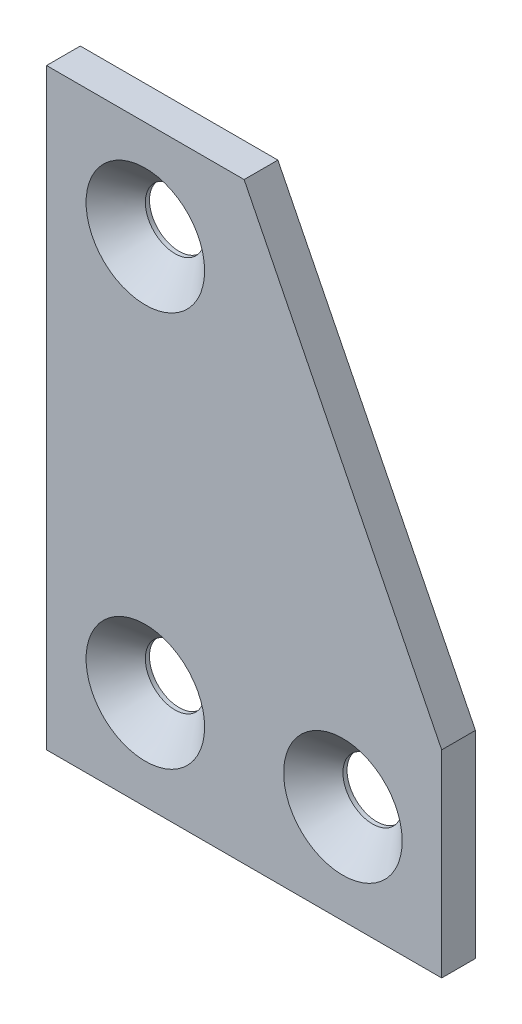
SolidWorks part; units mm, degrees
material "AISI 1010 Steel, hot rolled bar"
ref_plane "Front Plane" through (0, 0, 0) normal (0, 0, 1) x (1, 0, 0)
ref_plane "Top Plane" through (0, 0, 0) normal (0, 1, 0) x (1, 0, 0)
ref_plane "Right Plane" through (0, 0, 0) normal (1, 0, 0) x (0, 0, -1)
sketch "Sketch1" plane through (0, 0, 0) normal (0, 0, 1) x (1, 0, 0)
  line L2 (-20, -30) -> (-20, 30)
  line L3 (-20, 30) -> (0, 30)
  line L5 (-20, -30) -> (0, 30) construction
  line L6 (-20, -30) -> (20, -30)
  line L7 (20, -30) -> (20, -10)
  line L8 (0, 30) -> (20, -10)
  line L9 (0, 30) -> (0, -30) construction
  point P0 (0, 0)
  dimension "D1" = 60
  dimension "D2" = 20
  dimension "D3" = 40
  dimension "D4" = 20
extrude "Boss-Extrude1" add sketch "Sketch1" along normal mid plane 3.416
sketch "Sketch2" plane through (0, 0, 1.708) normal (0, 0, 1) x (1, 0, 0)
  line L0 (-10, 20) -> (-10, -20) construction
  line L1 (-10, -20) -> (10, -20) construction
  line L2 (10, -20) -> (10, 20) construction
  line L3 (10, 20) -> (-10, 20) construction
  line L4 (-10, 20) -> (10, -20) construction
  circle A0 centre (-10, 20) radius 3
  circle A1 centre (10, 20) radius 3
  circle A2 centre (-10, -20) radius 3
  circle A3 centre (10, -20) radius 3
  point P8 (0, 0)
  dimension "D1" = 6
  dimension "D2" = 40
  dimension "D3" = 20
extrude "Cut-Extrude1" cut sketch "Sketch2" against normal through all contours A0 | A2 | A3
chamfer "Chamfer1" distance 3 angle 45 3 edges at (13, -20, 1.708) (-7, -20, 1.708) (-7, 20, 1.708)
fillet "Fillet1" [suppressed] radius 1
